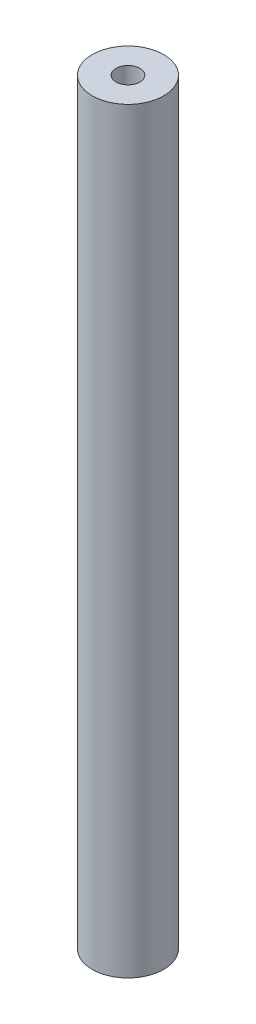
SolidWorks part; units mm, degrees
ref_plane "前视基准面" through (0, 0, 0) normal (0, 0, 1) x (1, 0, 0)
ref_plane "上视基准面" through (0, 0, 0) normal (0, 1, 0) x (1, 0, 0)
ref_plane "右视基准面" through (0, 0, 0) normal (1, 0, 0) x (0, 0, -1)
sketch "草图1" plane through (0, 0, 0) normal (0, 1, 0) x (1, 0, 0)
  circle A0 centre (0, 0) radius 3
  circle A1 centre (0, 0) radius 1
  dimension "D1" = 6
  dimension "D2" = 2
extrude "凸台-拉伸1" add sketch "草图1" along normal blind 63.5
